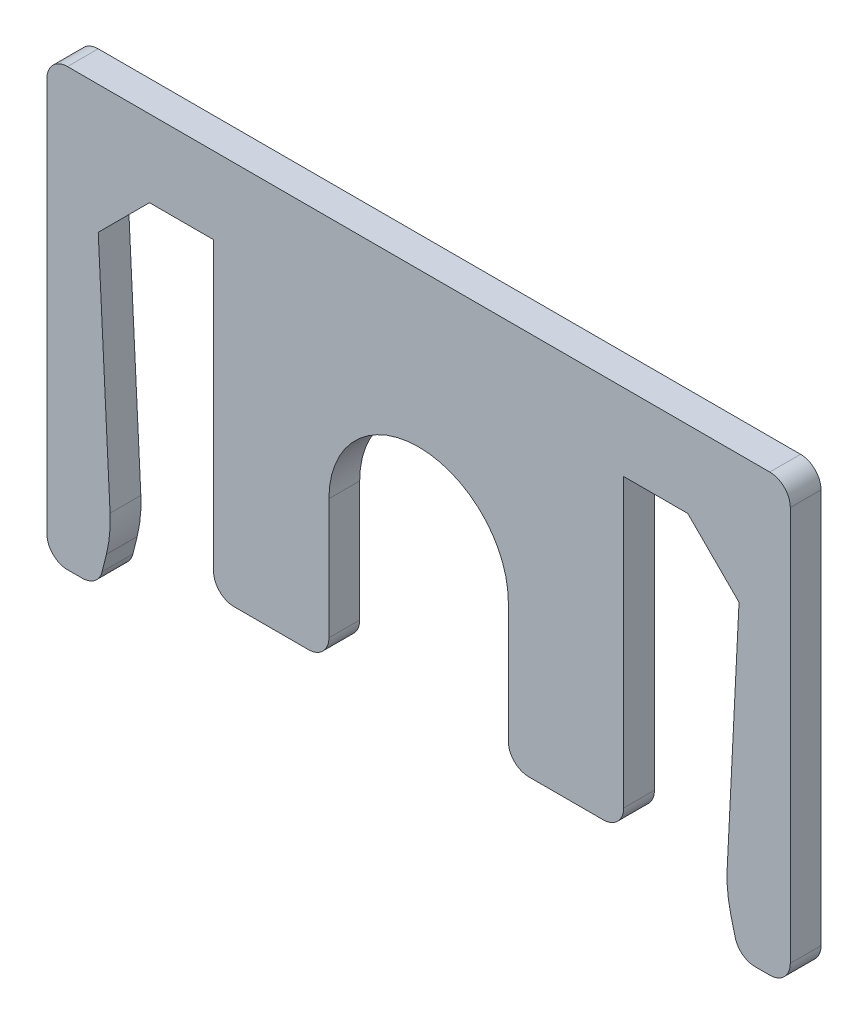
SolidWorks part; units mm, degrees
ref_plane "Front Plane" through (0, 0, 0) normal (0, 0, 1) x (1, 0, 0)
ref_plane "Top Plane" through (0, 0, 0) normal (0, 1, 0) x (1, 0, 0)
ref_plane "Right Plane" through (0, 0, 0) normal (1, 0, 0) x (0, 0, -1)
sketch "Sketch1" plane through (0, 0, 0) normal (0, 0, 1) x (1, 0, 0)
  line L0 (-12.5, 0) -> (-10.5, 0) construction
  line L1 (-10.5, 0) -> (-12.5, -2)
  line L2 (-12.5, -2) -> (-12.5, 0) construction
  line L3 (12.5, 0) -> (12.5, -2) construction
  line L4 (12.5, -2) -> (10.5, 0)
  line L5 (10.5, 0) -> (12.5, 0) construction
  line L6 (-12.5, -2) -> (-12, -12)
  line L7 (-12, -12) -> (-12.5, -14)
  line L8 (-12.5, -14) -> (-12.5, -2) construction
  line L9 (12.5, -2) -> (12.5, -14) construction
  line L10 (12.5, -14) -> (12, -12)
  line L11 (12, -12) -> (12.5, -2)
  line L12 (-10.5, 0) -> (-8, 0) construction
  line L13 (-3.5, -12) -> (3.5, -12) construction
  line L14 (-12.5, -14) -> (-14.5, -14)
  line L15 (-12.5, -14) -> (-12.5, -2) construction
  line L16 (-12.5, 3) -> (-14.5, 3)
  line L17 (-14.5, -14) -> (-14.5, 3)
  line L18 (12.5, -14) -> (14.5, -14)
  line L19 (12.5, -14) -> (12.5, -2) construction
  line L20 (12.5, 3) -> (14.5, 3)
  line L21 (14.5, -14) -> (14.5, 3)
  line L22 (-12.5, 3) -> (12.5, 3)
  line L23 (-12.5, 3) -> (-12.5, 0) construction
  line L24 (-10.5, 0) -> (-8, 0)
  line L25 (12.5, 3) -> (12.5, 0) construction
  line L26 (-3.5, -6.5) -> (3.5, -6.5) construction
  line L27 (-3.5, -6.5) -> (-3.5, -12)
  line L28 (-3.5, -12) -> (3.5, -12) construction
  line L29 (3.5, -6.5) -> (3.5, -12)
  line L30 (-8, -12) -> (-3.5, -12)
  line L31 (-8, -12) -> (-8, 0)
  line L32 (-8, 0) -> (8, 0) construction
  line L33 (8, -12) -> (8, 0)
  line L34 (-4.5, -3) -> (4.5, -3) construction
  line L35 (-4.5, -3) -> (-4.5, -12) construction
  line L36 (-4.5, -12) -> (-3.5, -12) construction
  line L37 (4.5, -3) -> (4.5, -12) construction
  line L38 (-4.5, -3) -> (4.5, -12) construction
  line L39 (-4.5, -12) -> (4.5, -3) construction
  line L40 (3.5, -12) -> (8, -12)
  line L41 (-3.5, -12) -> (3.5, -12) construction
  line L42 (3.5, -12) -> (4.5, -12) construction
  line L43 (-8, 0) -> (8, 0) construction
  line L44 (8, 0) -> (10.5, 0) construction
  line L45 (-8, 0) -> (8, 0) construction
  line L46 (8, 0) -> (10.5, 0)
  line L47 (-12.5, -2) -> (-12.5, 0) construction
  line L48 (-12.5, 0) -> (-12.5, 3) construction
  line L49 (-12.5, 0) -> (-10.5, 0) construction
  line L50 (12.5, 0) -> (12.5, 3) construction
  line L51 (10.5, 0) -> (12.5, 0) construction
  line L52 (12.5, -2) -> (12.5, 0) construction
  arc A0 (3.5, -6.5) -> (-3.5, -6.5) centre (0, -6.5) ccw
  arc A1 (-3.5, -6.5) -> (-1.9238, -9.4238) centre (0, -6.5) ccw construction
  arc A2 (-1.9238, -9.4238) -> (1.9238, -9.4238) centre (0, -6.5) ccw construction
  arc A3 (1.9238, -9.4238) -> (3.5, -6.5) centre (0, -6.5) ccw construction
  point P28 (0, 0)
  point P29 (0, -7.5)
  point P34 (5.8042, -3.4177)
  point P35 (-0.1925, -6.6497)
  point P37 (0, -6.898)
  point P38 (0, -7.5)
  point P39 (0, 0)
  point P40 (0, -7.5)
  point P41 (0, -5.5852)
  dimension "D12" = 7
  dimension "D1" = 2
  dimension "D2" = 2
  dimension "D3" = 2
  dimension "D4" = 0.5
  dimension "D5" = 2
  dimension "D6" = 10
  dimension "D7" = 0.5
  dimension "D8" = 21
  dimension "D9" = 2
  dimension "D10" = 2
  dimension "D11" = 3
  dimension "D13" = 16
  dimension "D14" = 9
  dimension "D15" = 9
  dimension "D16" = 10.5
  dimension "D17" = 1
extrude "Boss-Extrude1" add sketch "Sketch1" along normal blind 1.2
fillet "Fillet1" radius 5 2 edges at (-12, -12, 0.6) (12, -12, 0.6)
fillet "Fillet2" radius 0.8 10 edges at (14.5, 3, 0.6) (-14.5, 3, 0.6) (14.5, -14, 0.6) (-14.5, -14, 0.6) (12.5, -14, 0.6) (-12.5, -14, 0.6) (-8, -12, 0.6) (8, -12, 0.6) (3.5, -12, 0.6) (-3.5, -12, 0.6)
